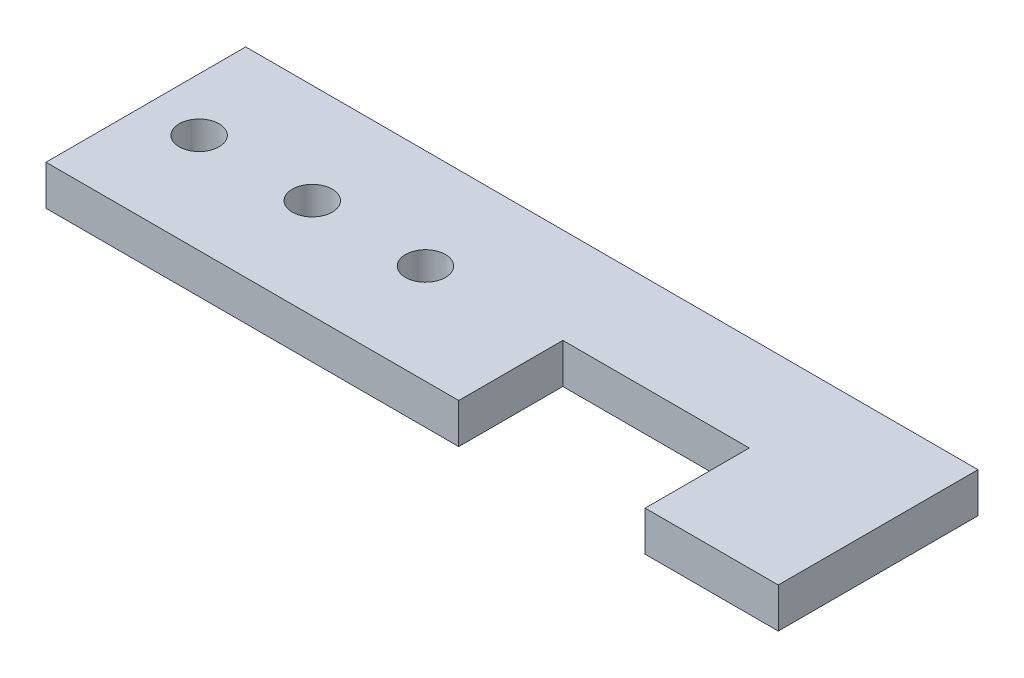
SolidWorks part; units mm, degrees
ref_plane "Plan de face" through (0, 0, 0) normal (0, 0, 1) x (1, 0, 0)
ref_plane "Plan de dessus" through (0, 0, 0) normal (0, 1, 0) x (1, 0, 0)
ref_plane "Plan de droite" through (0, 0, 0) normal (1, 0, 0) x (0, 0, -1)
sketch "Esquisse1" plane through (0, 0, 0) normal (0, 1, 0) x (1, 0, 0)
  line L0 (31, 0) -> (31, 7.8203)
  line L1 (0, 0) -> (55, 0)
  line L2 (0, 0) -> (0, 15)
  line L3 (0, 15) -> (55, 15)
  line L4 (55, 0) -> (55, 15)
  line L5 (31, 7.8203) -> (45, 7.8203)
  line L6 (45, 7.8203) -> (45, 0)
  circle A0 centre (4, 7.5) radius 1.5
  circle A1 centre (12.5, 7.5) radius 1.5
  circle A2 centre (21, 7.5) radius 1.5
  dimension "D3" = 3
  dimension "D4" = 3
  dimension "D5" = 3
  dimension "D12" = 7.5
  dimension "D1" = 55
  dimension "D2" = 15
  dimension "D6" = 8.5
  dimension "D7" = 0
  dimension "D8" = 8.5
  dimension "D9" = 14
  dimension "D10" = 10
  dimension "D11" = 4
extrude "Boss.-Extru.2" add sketch "Esquisse1" along normal blind 3 contours L5 L6 L1 L4 L3 L2 L0 A2 A1 A0
